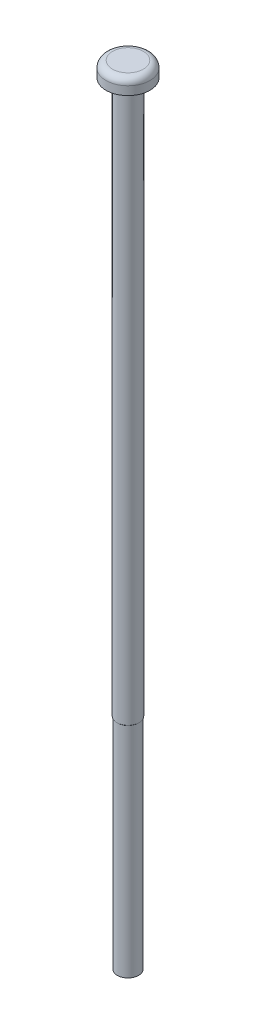
SolidWorks part; units mm, degrees
ref_plane "Alzado" through (0, 0, 0) normal (0, 0, 1) x (1, 0, 0)
ref_plane "Planta" through (0, 0, 0) normal (0, 1, 0) x (1, 0, 0)
ref_plane "Vista lateral" through (0, 0, 0) normal (1, 0, 0) x (0, 0, -1)
sketch "Croquis1" plane through (0, 0, 0) normal (0, 0, 1) x (1, 0, 0)
  line L0 (0, 120) -> (0, 0)
  line L1 (0, 120) -> (-2.35, 120)
  line L2 (-3.35, 119) -> (-3.35, 117.7)
  line L3 (-3.35, 117.7) -> (-1.7, 117.7)
  line L4 (-1.7, 117.7) -> (-1.7, 33.4)
  line L5 (-1.7, 33.4) -> (-1.6296, 33.3296)
  line L6 (-1.6296, 33.3296) -> (-1.6296, 0)
  line L7 (-1.6296, 0) -> (0, 0)
  arc A0 (-3.35, 119) -> (-2.35, 120) centre (-2.35, 119) cw
  dimension "D6" = 1
  dimension "D1" = 120
  dimension "D2" = 1.7
  dimension "D3" = 3.35
  dimension "D4" = 2.3
  dimension "D5" = 33.4
revolve "Revolución1" add sketch "Croquis1" angle 360 about L0
